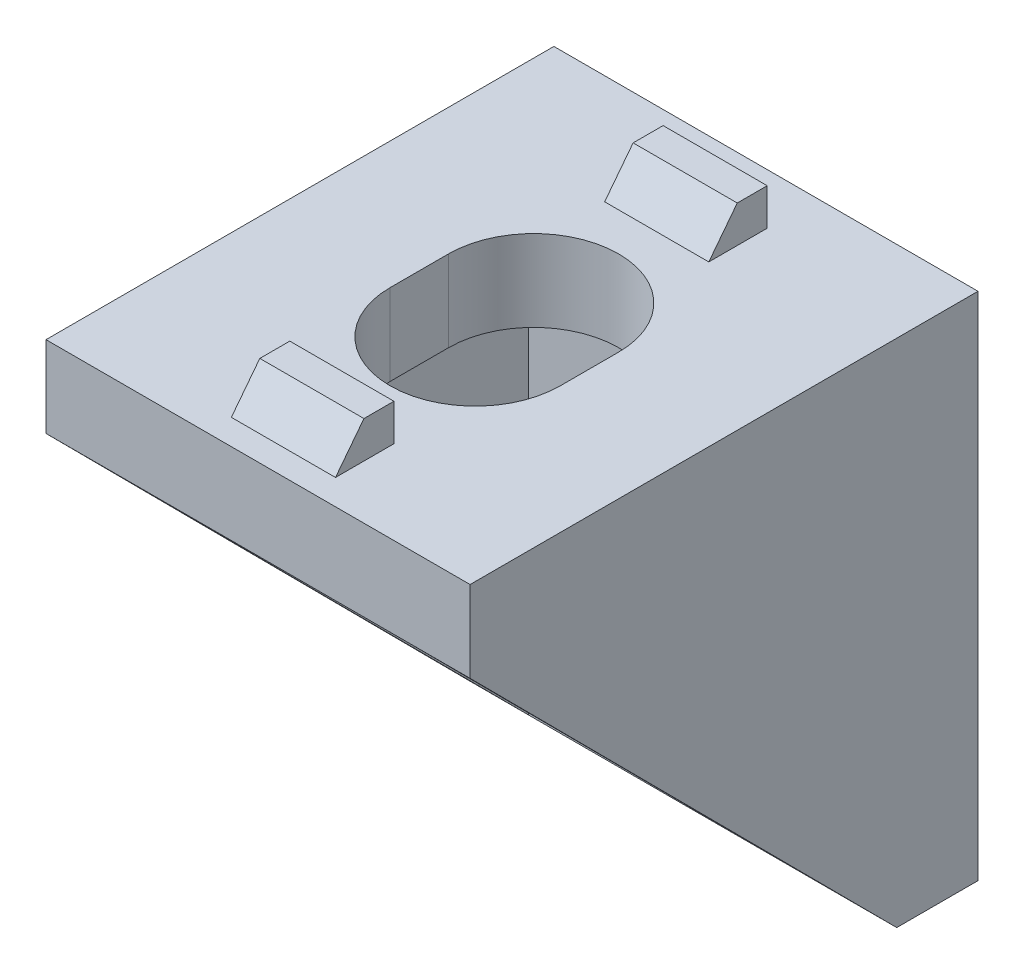
SolidWorks part; units mm, degrees
ref_plane "Alzado" through (0, 0, 0) normal (0, 0, 1) x (1, 0, 0)
ref_plane "Planta" through (0, 0, 0) normal (0, 1, 0) x (1, 0, 0)
ref_plane "Vista lateral" through (0, 0, 0) normal (1, 0, 0) x (0, 0, -1)
sketch "Croquis1" plane through (0, 0, 0) normal (0, 0, 1) x (1, 0, 0)
  line L1 (-8.35, -10.05) -> (8.35, -10.05)
  line L2 (-8.35, -10.05) -> (-8.35, 10.05)
  line L3 (-8.35, 10.05) -> (8.35, 10.05)
  line L4 (8.35, -10.05) -> (8.35, 10.05)
  line L5 (-8.35, -10.05) -> (8.35, 10.05) construction
  line L6 (-8.35, 10.05) -> (8.35, -10.05) construction
  point P0 (0, 0)
  dimension "D1" = 16.7
  dimension "D2" = 20.1
extrude "Saliente-Extruir1" add sketch "Croquis1" along normal blind 3.2
sketch "Croquis2" plane through (-8.35, 0, 0) normal (-1, 0, 0) x (0, 0, 1)
  line L0 (0, 10.05) -> (20, 10.05)
  line L1 (20, 10.05) -> (20, 6.85)
  line L2 (20, 6.85) -> (0, 6.85)
  line L3 (0, 10.05) -> (0, -10.05) construction
  line L4 (0, 6.85) -> (0, 10.05)
  dimension "D1" = 20
  dimension "D2" = 3.2
extrude "Saliente-Extruir2" add sketch "Croquis2" against normal blind 16.7
sketch "Croquis3" plane through (-8.35, 0, 0) normal (-1, 0, 0) x (0, 0, 1)
  line L0 (20, 6.85) -> (3.2, -10.05)
  line L1 (3.2, -10.05) -> (3.2, 6.85)
  line L2 (3.2, 6.85) -> (20, 6.85)
extrude "Saliente-Extruir3" add sketch "Croquis3" against normal blind 2.2
sketch "Croquis4" plane through (8.35, 0, 0) normal (1, 0, 0) x (0, 0, -1)
  line L0 (-20, 6.85) -> (-3.2, -10.05)
  line L1 (-3.2, -10.05) -> (-3.2, 6.85)
  line L2 (-3.2, 6.85) -> (-20, 6.85)
extrude "Saliente-Extruir4" add sketch "Croquis4" against normal blind 2.2
sketch "Croquis5" plane through (0, 0, 0) normal (0, 0, -1) x (-1, 0, 0)
  line L0 (-3.35, 1.5) -> (3.35, 1.5)
  line L1 (3.35, 1.5) -> (3.35, -0.9)
  line L2 (3.35, -0.9) -> (-3.35, -0.9)
  line L3 (-3.35, -0.9) -> (-3.35, 1.5)
  line L4 (-8.35, -10.05) -> (-8.35, 10.05) construction
  line L6 (8.35, -10.05) -> (-8.35, -10.05) construction
  line L7 (8.35, 10.05) -> (8.35, -10.05) construction
  line L8 (-8.35, 10.05) -> (8.35, 10.05) construction
  arc A0 (-3.35, 1.5) -> (3.35, 1.5) centre (0, 1.5) cw
  arc A1 (-3.35, -0.9) -> (3.35, -0.9) centre (0, -0.9) ccw
  point P10 (0, -4.25)
  point P15 (0, 4.85)
  point P18 (0, 10.05)
  dimension "D2" = 5.8
  dimension "D1" = 5
  dimension "D3" = 5
  dimension "D4" = 5.2
extrude "Cortar-Extruir1" cut sketch "Croquis5" against normal blind 3.2 contours A0 L0 | L3 L2 L1 L0 | L2 A1
sketch "Croquis6" plane through (0, 10.05, 0) normal (0, 1, 0) x (1, 0, 0)
  line L0 (-3.35, -9.15) -> (3.35, -9.15)
  line L1 (3.35, -9.15) -> (3.35, -11.45)
  line L2 (3.35, -11.45) -> (-3.35, -11.45)
  line L3 (-3.35, -11.45) -> (-3.35, -9.15)
  line L4 (-8.35, -20) -> (-8.35, 0) construction
  line L5 (8.35, -20) -> (8.35, 0) construction
  line L7 (8.35, -20) -> (-8.35, -20) construction
  arc A0 (-3.35, -9.15) -> (3.35, -9.15) centre (0, -9.15) cw
  arc A1 (-3.35, -11.45) -> (3.35, -11.45) centre (0, -11.45) ccw
  point P12 (0, -5.8)
  point P14 (0, -14.8)
  dimension "D4" = 5.2
  dimension "D1" = 5
  dimension "D2" = 5
  dimension "D3" = 5.8
extrude "Cortar-Extruir2" cut sketch "Croquis6" against normal blind 3.2 contours A0 L0 | L3 L2 L1 L0 | L2 A1
sketch "Croquis7" plane through (0, 0, 0) normal (0, 0, -1) x (-1, 0, 0)
  line L0 (-2.05, -9.05) -> (2.05, -9.05)
  line L1 (-2.05, 8.05) -> (2.05, 8.05)
  line L2 (-8.35, 10.05) -> (8.35, 10.05) construction
  line L3 (8.35, -10.05) -> (-8.35, -10.05) construction
  line L4 (-8.35, -10.05) -> (-8.35, 10.05) construction
  line L5 (8.35, 10.05) -> (8.35, -10.05) construction
  line L6 (-2.05, -9.05) -> (-2.05, -6.75)
  line L7 (-2.05, -6.75) -> (2.05, -6.75)
  line L8 (2.05, -6.75) -> (2.05, -9.05)
  line L9 (-2.05, -7.93) -> (2.05, -7.93)
  line L10 (-2.05, 8.05) -> (-2.05, 5.75)
  line L11 (-2.05, 5.75) -> (2.05, 5.75)
  line L12 (2.05, 5.75) -> (2.05, 8.05)
  line L13 (-2.05, 6.87) -> (2.05, 6.87)
  dimension "D1" = 2
  dimension "D2" = 1
  dimension "D3" = 6.3
  dimension "D4" = 6.3
  dimension "D5" = 6.3
  dimension "D6" = 6.3
  dimension "D7" = 2.3
  dimension "D8" = 1.18
  dimension "D9" = 2.3
  dimension "D10" = 1.18
extrude "Saliente-Extruir9" add sketch "Croquis7" along normal blind 1.45 contours L10 L13 L12 L1 | L6 L9 L8 L7
sketch "Croquis9" plane through (-2.05, 0, 0) normal (-1, 0, 0) x (0, 0, 1)
  line L0 (-1.45, 6.87) -> (0, 5.75)
  line L1 (0, 10.05) -> (0, -10.05) construction
  line L2 (0, 5.75) -> (0, 6.87)
  line L3 (0, 6.87) -> (-1.45, 6.87)
  line L4 (-1.45, -7.93) -> (0, -9.05)
  line L5 (0, -9.05) -> (0, -7.93)
  line L6 (0, -7.93) -> (-1.45, -7.93)
  dimension "D1" = 1.12
  dimension "D2" = 1
extrude "Saliente-Extruir10" add sketch "Croquis9" against normal blind 4.1
sketch "Croquis10" plane through (0, 10.05, 0) normal (0, 1, 0) x (1, 0, 0)
  line L0 (-2.05, -2) -> (2.0489, -2)
  line L2 (8.35, 0) -> (-8.35, 0) construction
  line L3 (-8.35, -20) -> (-8.35, 0) construction
  line L4 (8.35, -20) -> (8.35, 0) construction
  line L5 (-2.05, -19) -> (2.0489, -19)
  line L6 (8.35, -20) -> (-8.35, -20) construction
  line L7 (-2.05, -19) -> (-2.05, -16.7)
  line L8 (-2.05, -16.7) -> (2.0489, -16.7)
  line L9 (2.0489, -16.7) -> (2.0489, -19)
  line L10 (-2.05, -2) -> (-2.05, -4.3)
  line L11 (-2.05, -4.3) -> (2.0489, -4.3)
  line L12 (2.0489, -4.3) -> (2.0489, -2)
  line L13 (-2.05, -3.18) -> (2.0489, -3.18)
  line L14 (-2.05, -17.88) -> (2.0489, -17.88)
  dimension "D1" = 2
  dimension "D2" = 6.3
  dimension "D3" = 6.3011
  dimension "D4" = 6.3
  dimension "D5" = 6.3011
  dimension "D6" = 1
  dimension "D7" = 2.3
  dimension "D8" = 2.3
  dimension "D9" = 1.18
  dimension "D10" = 1.18
extrude "Saliente-Extruir13" add sketch "Croquis10" along normal blind 1.45 contours L10 L13 L12 L0 | L7 L14 L9 L8
sketch "Croquis12" plane through (2.0489, 0, 0) normal (1, 0, 0) x (0, 0, -1)
  line L0 (-17.88, 11.5) -> (-19, 10.05)
  line L1 (-20, 10.05) -> (0, 10.05) construction
  line L2 (-19, 10.05) -> (-17.88, 10.05)
  line L3 (-17.88, 10.05) -> (-17.88, 11.5)
  line L4 (-3.18, 11.5) -> (-4.3, 10.05)
  line L5 (-4.3, 10.05) -> (-3.18, 10.05)
  line L6 (-3.18, 10.05) -> (-3.18, 11.5)
  dimension "D1" = 1
extrude "Saliente-Extruir14" add sketch "Croquis12" against normal blind 4.1
sketch "Croquis13" plane through (-2.05, 0, 0) normal (-1, 0, 0) x (0, 0, 1)
  line L0 (2, 11.5) -> (2, 10.05)
  line L1 (2, 10.05) -> (4.3, 10.05)
  line L2 (4.3, 10.05) -> (3.18, 11.5)
  line L3 (3.18, 11.5) -> (2, 11.5)
  line L4 (16.7, 11.5) -> (16.7, 10.05)
  line L5 (16.7, 10.05) -> (19, 10.05)
  line L6 (19, 10.05) -> (17.88, 11.5)
  line L7 (17.88, 11.5) -> (16.7, 11.5)
extrude "Saliente-Extruir16" add sketch "Croquis13" against normal blind 4.1
